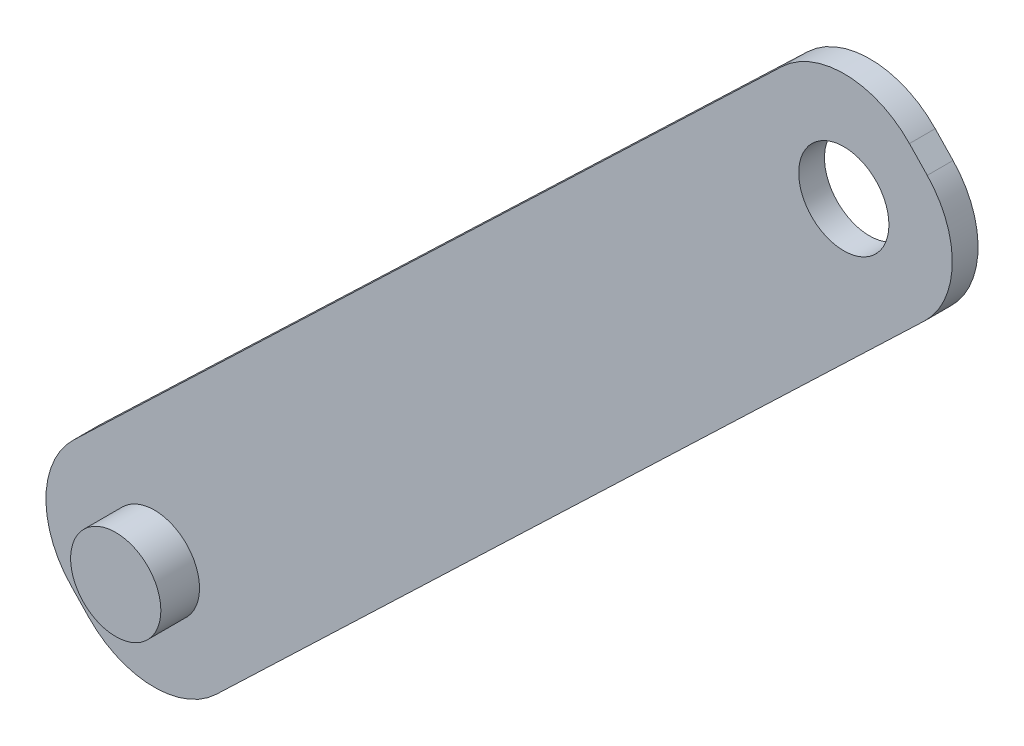
SolidWorks part; units mm, degrees
ref_plane "Front Plane" through (0, 0, 0) normal (0, 0, 1) x (1, 0, 0)
ref_plane "Top Plane" through (0, 0, 0) normal (0, 1, 0) x (1, 0, 0)
ref_plane "Right Plane" through (0, 0, 0) normal (1, 0, 0) x (0, 0, -1)
sketch "Sketch1" plane through (0, 0, 0) normal (0, 0, 1) x (1, 0, 0)
  line L0 (-124.2674, 0) -> (124.2674, 0) construction
  line L1 (0, 74.7504) -> (0, -74.7504) construction
  line L2 (21.9311, 32.1829) -> (-32.9905, -20.3492)
  line L3 (-33.2106, -30.2462) -> (-31.8281, -31.6915)
  line L4 (-21.9311, -31.9116) -> (32.9905, 20.6205)
  line L5 (33.2106, 30.5176) -> (31.8281, 31.9629)
  arc A0 (-32.9905, -20.3492) -> (-33.2106, -30.2462) centre (-28.152, -25.4077) ccw
  arc A1 (-31.8281, -31.6915) -> (-21.9311, -31.9116) centre (-26.7696, -26.853) ccw
  arc A2 (32.9905, 20.6205) -> (33.2106, 30.5176) centre (28.152, 25.6791) ccw
  arc A3 (31.8281, 31.9629) -> (21.9311, 32.1829) centre (26.7696, 27.1244) ccw
  arc A4 (-29.2674, -27.8584) -> (-24.2088, -23.0199) centre (-26.7381, -25.4392) ccw
  arc A5 (-24.2088, -23.0199) -> (-29.2674, -27.8584) centre (-26.7381, -25.4392) ccw
  arc A6 (24.2088, 23.2913) -> (29.2674, 28.1297) centre (26.7381, 25.7105) ccw
  arc A7 (29.2674, 28.1297) -> (24.2088, 23.2913) centre (26.7381, 25.7105) ccw
  point P4 (0, 0)
  point P8 (0, 0)
extrude "Boss-Extrude2" add sketch "Sketch1" along normal blind 2 contours L5 A3 L2 A0 L3 A1 L4 A2 A7 A6 A5 A4 | A4 A5
sketch "Sketch2" plane through (0, 0, 2) normal (0, 0, 1) x (1, 0, 0)
  circle A0 centre (-26.7381, -25.4392) radius 3.5
extrude "Boss-Extrude3" add sketch "Sketch2" along normal blind 3
